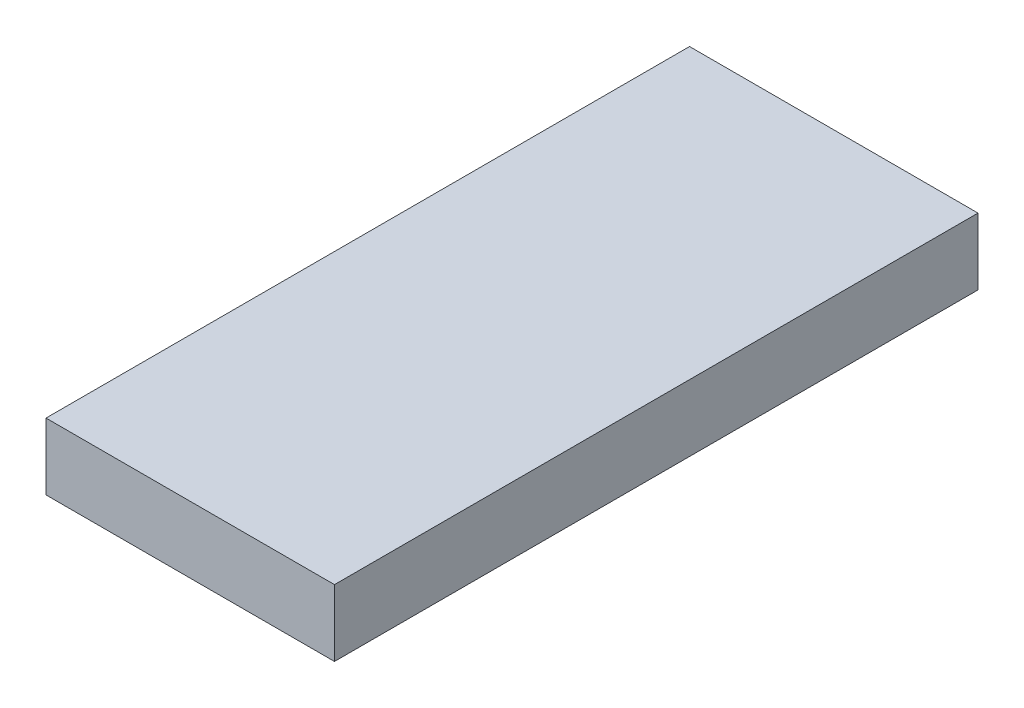
SolidWorks part; units mm, degrees
ref_plane "Front Plane" through (0, 0, 0) normal (0, 0, 1) x (1, 0, 0)
ref_plane "Top Plane" through (0, 0, 0) normal (0, 1, 0) x (1, 0, 0)
ref_plane "Right Plane" through (0, 0, 0) normal (1, 0, 0) x (0, 0, -1)
sketch "Sketch1" plane through (0, 0, 0) normal (0, 1, 0) x (1, 0, 0)
  line L1 (-34.5167, 19.53) -> (46.7333, 19.53)
  line L2 (-34.5167, 19.53) -> (-34.5167, -161.72)
  line L3 (-34.5167, -161.72) -> (46.7333, -161.72)
  line L4 (46.7333, 19.53) -> (46.7333, -161.72)
  dimension "D1" = 81.25
  dimension "D2" = 181.25
extrude "Boss-Extrude1" add sketch "Sketch1" along normal blind 18.75
